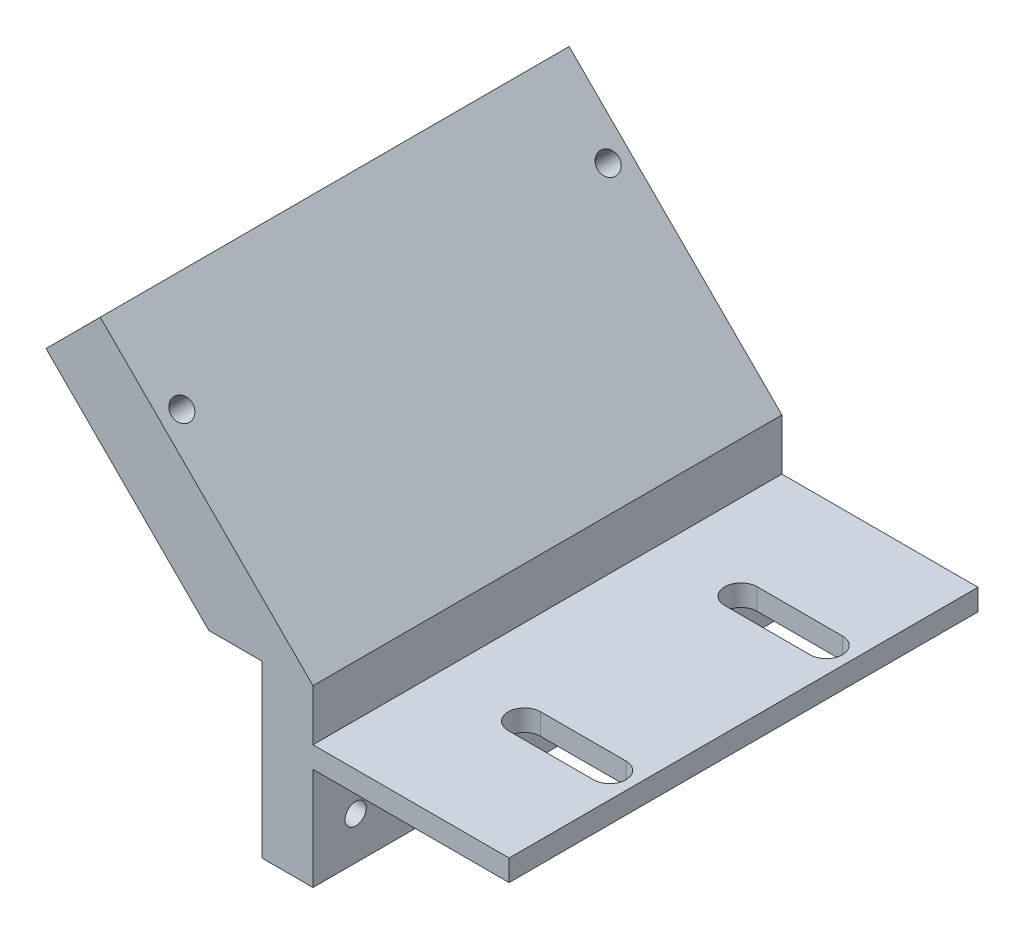
SolidWorks part; units mm, degrees
ref_plane "Front Plane" through (0, 0, 0) normal (0, 0, 1) x (1, 0, 0)
ref_plane "Top Plane" through (0, 0, 0) normal (0, 1, 0) x (1, 0, 0)
ref_plane "Right Plane" through (0, 0, 0) normal (1, 0, 0) x (0, 0, -1)
sketch "Sketch1" plane through (0, 0, 0) normal (0, 0, 1) x (1, 0, 0)
  line L0 (0, 0) -> (-23, 0)
  line L4 (-23, 2.5) -> (0, 2.5)
  line L5 (0, 2.5) -> (0, 0)
  line L13 (-23, 0) -> (-23, -12)
  line L14 (-23, -12) -> (-29, -12)
  line L15 (-29, -12) -> (-29, 8)
  line L16 (-29, 8) -> (-35.2279, 8)
  line L17 (-35.2279, 8) -> (-54.3198, 27.0919)
  line L18 (-54.3198, 27.0919) -> (-47.9558, 33.4558)
  line L19 (-47.9558, 33.4558) -> (-23, 8.5)
  line L20 (-23, 8.5) -> (-23, 2.5)
  point P4 (-17.5315, 2.5)
  point P13 (-23, 2.5)
  point P14 (-23.5875, 5.2368)
  dimension "D1" = 23
  dimension "D2" = 9
  dimension "D3" = 6
  dimension "D4" = 2.5
  dimension "D5" = 45
  dimension "D6" = 6
  dimension "D7" = 20
  dimension "D8" = 27
  dimension "D9" = 12
extrude "Boss-Extrude1" add sketch "Sketch1" along normal mid plane 55
sketch "Sketch3" plane through (0, 2.5, 0) normal (0, 1, 0) x (1, 0, 0)
  line L0 (-13, -12.7) -> (-3, -12.7) construction
  line L1 (-13, -10.795) -> (-3, -10.795)
  line L2 (-13, -14.605) -> (-3, -14.605)
  line L3 (-22.4407, 0) -> (10.5779, 0) construction
  line L4 (-13, 12.7) -> (-3, 12.7) construction
  line L5 (-13, 10.795) -> (-3, 10.795)
  line L6 (-13, 14.605) -> (-3, 14.605)
  arc A0 (-13, -10.795) -> (-13, -14.605) centre (-13, -12.7) ccw
  arc A1 (-3, -14.605) -> (-3, -10.795) centre (-3, -12.7) ccw
  arc A2 (-13, 10.795) -> (-13, 14.605) centre (-13, 12.7) cw
  arc A3 (-3, 14.605) -> (-3, 10.795) centre (-3, 12.7) cw
  point P2 (-8, -12.7)
  point P12 (-8, 12.7)
  dimension "D1" = 1.905
  dimension "D3" = 3
  dimension "D2" = 10
  dimension "D4" = 14.605
extrude "Cut-Extrude2" cut sketch "Sketch3" against normal up to next
sketch "Sketch4" plane through (-23, 0, 0) normal (1, 0, 0) x (0, 0, -1)
  line L0 (-22.5, -7) -> (-27.5, -7) construction
  line L1 (-27.5, -12) -> (-27.5, 0) construction
  line L2 (22.5, -7) -> (27.5, -7) construction
  line L3 (27.5, -12) -> (27.5, 0) construction
  line L4 (-27.5, -12) -> (27.5, -12) construction
  circle A0 centre (-22.5, -7) radius 1.25
  circle A1 centre (22.5, -7) radius 1.25
  point P12 (0, 0)
  dimension "D1" = 2.5
  dimension "D2" = 45
  dimension "D3" = 5
extrude "Cut-Extrude3" cut sketch "Sketch4" against normal up to next
sketch "Sketch5" plane through (-7.25, -7.25, 0) normal (0.7071, 0.7071, 0) x (0, 0, -1)
  line L0 (-25, 47.5668) -> (-27.5, 47.5668) construction
  line L1 (-27.5, 22.2739) -> (-27.5, 57.5668) construction
  line L2 (25, 47.5668) -> (27.5, 47.5668) construction
  line L3 (27.5, 22.2739) -> (27.5, 57.5668) construction
  line L4 (-27.5, 57.5668) -> (27.5, 57.5668) construction
  circle A0 centre (-25, 47.5668) radius 1.25
  circle A1 centre (25, 47.5668) radius 1.25
  point P10 (0, 0)
  dimension "D1" = 2.5
  dimension "D2" = 10
  dimension "D3" = 50
extrude "Cut-Extrude4" cut sketch "Sketch5" against normal up to next
